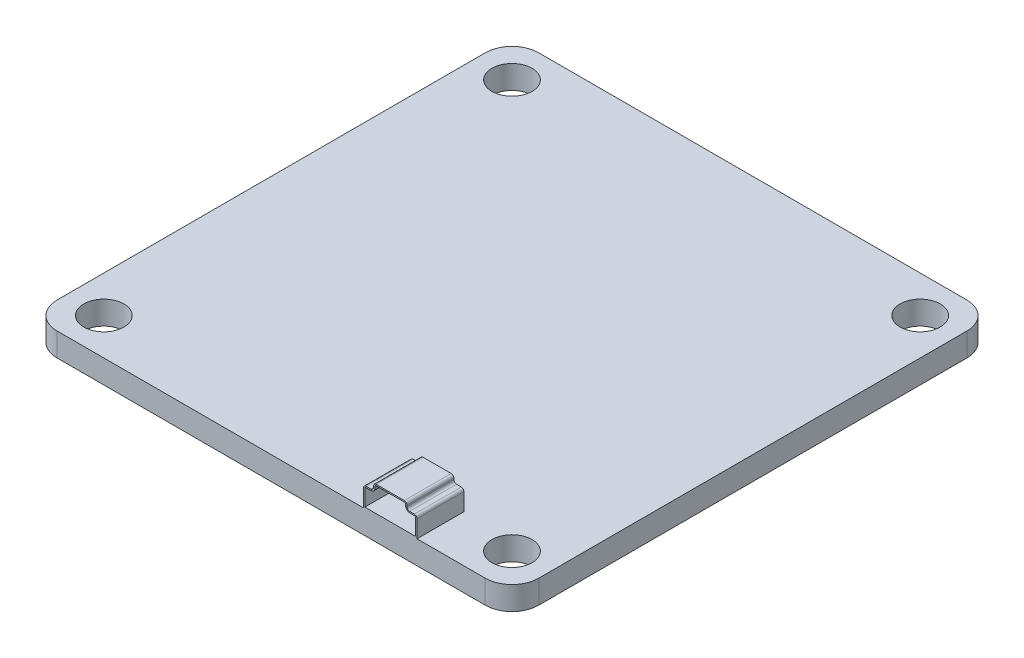
SolidWorks part; units mm, degrees
ref_plane "Front Plane" through (0, 0, 0) normal (0, 0, 1) x (1, 0, 0)
ref_plane "Top Plane" through (0, 0, 0) normal (0, 1, 0) x (1, 0, 0)
ref_plane "Right Plane" through (0, 0, 0) normal (1, 0, 0) x (0, 0, -1)
sketch "Sketch1" plane through (0, 0, 0) normal (0, 1, 0) x (1, 0, 0)
  line L1 (16, -18) -> (-16, -18)
  line L2 (18, -16) -> (18, 16)
  line L3 (16, 18) -> (-16, 18)
  line L4 (-18, -16) -> (-18, 16)
  line L5 (18, -18) -> (-18, 18) construction
  line L6 (18, 18) -> (-18, -18) construction
  line L7 (-15.25, -15.25) -> (15.25, -15.25) construction
  line L8 (-15.25, -15.25) -> (-15.25, 15.25) construction
  line L9 (-15.25, 15.25) -> (15.25, 15.25) construction
  line L10 (15.25, -15.25) -> (15.25, 15.25) construction
  line L11 (-15.25, -15.25) -> (15.25, 15.25) construction
  line L12 (-15.25, 15.25) -> (15.25, -15.25) construction
  circle A0 centre (-15.25, 15.25) radius 1.5
  circle A1 centre (15.25, 15.25) radius 1.5
  circle A2 centre (15.25, -15.25) radius 1.5
  circle A3 centre (-15.25, -15.25) radius 1.5
  arc A4 (-16, -18) -> (-18, -16) centre (-16, -16) cw
  arc A5 (16, -18) -> (18, -16) centre (16, -16) ccw
  arc A6 (18, 16) -> (16, 18) centre (16, 16) ccw
  arc A7 (-16, 18) -> (-18, 16) centre (-16, 16) ccw
  point P0 (0, 0)
  point P6 (0, 0)
  dimension "D4" = 3
  dimension "D5" = 2
  dimension "D1" = 36
  dimension "D2" = 36
  dimension "D3" = 30.5
extrude "Boss-Extrude3" add sketch "Sketch1" along normal blind 1.75
sketch "Sketch6" plane through (-4.3265, 0, 18) normal (0, 0, 1) x (1, 0, 0)
  line L1 (11.2305, 1.75) -> (15.2305, 1.75)
  line L2 (11.2305, 1.75) -> (11.2305, 3.0502)
  line L3 (12.1805, 3.75) -> (14.2805, 3.75)
  line L4 (15.2305, 1.75) -> (15.2305, 3.0502)
  line L5 (11.9805, 3.55) -> (11.9805, 3.4502)
  line L6 (11.7805, 3.2502) -> (11.4305, 3.2502)
  line L7 (14.4805, 3.55) -> (14.4805, 3.4502)
  line L8 (14.6805, 3.2502) -> (15.0305, 3.2502)
  line L9 (12.1805, 3.65) -> (14.2805, 3.65)
  line L10 (14.3805, 3.55) -> (14.3805, 3.4502)
  line L11 (14.6805, 3.1502) -> (15.0305, 3.1502)
  line L12 (15.1305, 1.85) -> (15.1305, 3.0502)
  line L13 (11.3305, 1.85) -> (15.1305, 1.85)
  line L14 (11.3305, 1.85) -> (11.3305, 3.0502)
  line L15 (11.7805, 3.1502) -> (11.4305, 3.1502)
  line L16 (12.0805, 3.55) -> (12.0805, 3.4502)
  line L17 (18.0765, 0) -> (21.0765, 0) construction
  arc A0 (15.0305, 3.2502) -> (15.2305, 3.0502) centre (15.0305, 3.0502) cw
  arc A1 (14.4805, 3.4502) -> (14.6805, 3.2502) centre (14.6805, 3.4502) ccw
  arc A2 (14.4805, 3.55) -> (14.2805, 3.75) centre (14.2805, 3.55) ccw
  arc A3 (11.9805, 3.55) -> (12.1805, 3.75) centre (12.1805, 3.55) cw
  arc A4 (11.9805, 3.4502) -> (11.7805, 3.2502) centre (11.7805, 3.4502) cw
  arc A5 (11.4305, 3.2502) -> (11.2305, 3.0502) centre (11.4305, 3.0502) ccw
  arc A6 (14.3805, 3.55) -> (14.2805, 3.65) centre (14.2805, 3.55) ccw
  arc A7 (14.3805, 3.4502) -> (14.6805, 3.1502) centre (14.6805, 3.4502) ccw
  arc A8 (15.0305, 3.1502) -> (15.1305, 3.0502) centre (15.0305, 3.0502) cw
  arc A9 (11.4305, 3.1502) -> (11.3305, 3.0502) centre (11.4305, 3.0502) ccw
  arc A10 (12.0805, 3.4502) -> (11.7805, 3.1502) centre (11.7805, 3.4502) cw
  arc A11 (12.0805, 3.55) -> (12.1805, 3.65) centre (12.1805, 3.55) cw
  dimension "D1" = 0.2
  dimension "D2" = 0.1
extrude "Boss-Extrude4" add sketch "Sketch6" against normal blind 3.0021
sketch "Sketch7" plane through (0, 0, 14.9979) normal (0, 0, -1) x (-1, 0, 0)
  line L8 (-6.9041, 1.75) -> (-6.9041, 3.0502)
  line L9 (-7.1041, 3.2502) -> (-7.4541, 3.2502)
  line L10 (-7.6541, 3.4502) -> (-7.6541, 3.55)
  line L11 (-7.8541, 3.75) -> (-9.9541, 3.75)
  line L12 (-10.1541, 3.55) -> (-10.1541, 3.4502)
  line L13 (-10.3541, 3.2502) -> (-10.7041, 3.2502)
  line L14 (-10.9041, 3.0502) -> (-10.9041, 1.75)
  line L15 (-10.9041, 1.75) -> (-6.9041, 1.75)
  line L16 (-6.9041, 1.75) -> (-6.9041, 3.0502)
  line L17 (-7.1041, 3.2502) -> (-7.4541, 3.2502)
  line L18 (-7.6541, 3.4502) -> (-7.6541, 3.55)
  line L19 (-7.8541, 3.75) -> (-9.9541, 3.75)
  line L20 (-10.1541, 3.55) -> (-10.1541, 3.4502)
  line L21 (-10.3541, 3.2502) -> (-10.7041, 3.2502)
  line L22 (-10.9041, 3.0502) -> (-10.9041, 1.75)
  line L23 (-10.9041, 1.75) -> (-6.9041, 1.75)
  arc A6 (-6.9041, 3.0502) -> (-7.1041, 3.2502) centre (-7.1041, 3.0502) ccw
  arc A7 (-7.6541, 3.4502) -> (-7.4541, 3.2502) centre (-7.4541, 3.4502) ccw
  arc A8 (-7.6541, 3.55) -> (-7.8541, 3.75) centre (-7.8541, 3.55) ccw
  arc A9 (-9.9541, 3.75) -> (-10.1541, 3.55) centre (-9.9541, 3.55) ccw
  arc A10 (-10.3541, 3.2502) -> (-10.1541, 3.4502) centre (-10.3541, 3.4502) ccw
  arc A11 (-10.7041, 3.2502) -> (-10.9041, 3.0502) centre (-10.7041, 3.0502) ccw
  arc A12 (-6.9041, 3.0502) -> (-7.1041, 3.2502) centre (-7.1041, 3.0502) ccw
  arc A13 (-7.6541, 3.4502) -> (-7.4541, 3.2502) centre (-7.4541, 3.4502) ccw
  arc A14 (-7.6541, 3.55) -> (-7.8541, 3.75) centre (-7.8541, 3.55) ccw
  arc A15 (-9.9541, 3.75) -> (-10.1541, 3.55) centre (-9.9541, 3.55) ccw
  arc A16 (-10.3541, 3.2502) -> (-10.1541, 3.4502) centre (-10.3541, 3.4502) ccw
  arc A17 (-10.7041, 3.2502) -> (-10.9041, 3.0502) centre (-10.7041, 3.0502) ccw
  dimension "D1" = 0
extrude "Boss-Extrude5" add sketch "Sketch7" along normal blind 0.5
